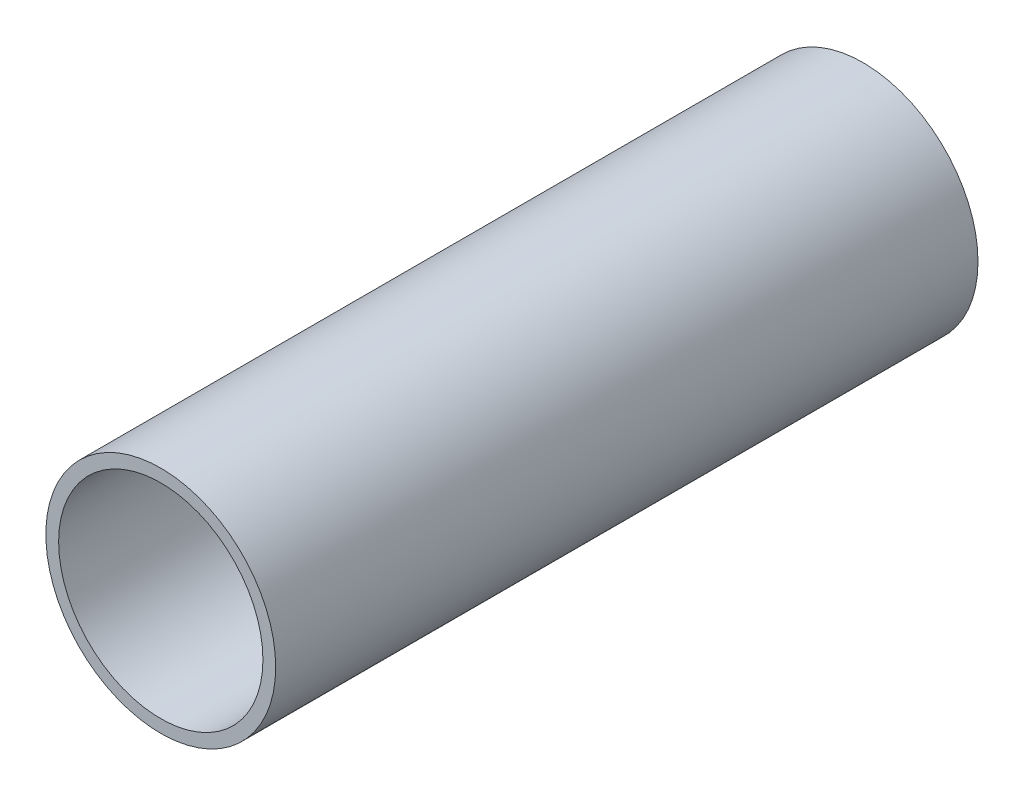
SolidWorks part; units mm, degrees
ref_plane "Front Plane" through (0, 0, 0) normal (0, 0, 1) x (1, 0, 0)
ref_plane "Top Plane" through (0, 0, 0) normal (0, 1, 0) x (1, 0, 0)
ref_plane "Right Plane" through (0, 0, 0) normal (1, 0, 0) x (0, 0, -1)
sketch "Sketch1" plane through (0, 0, 0) normal (0, 0, 1) x (1, 0, 0)
  circle A0 centre (0, 0) radius 16
  circle A1 centre (0, 0) radius 18
  dimension "D1" = 32
  dimension "D2" = 2
extrude "Boss-Extrude1" add sketch "Sketch1" along normal blind 110
